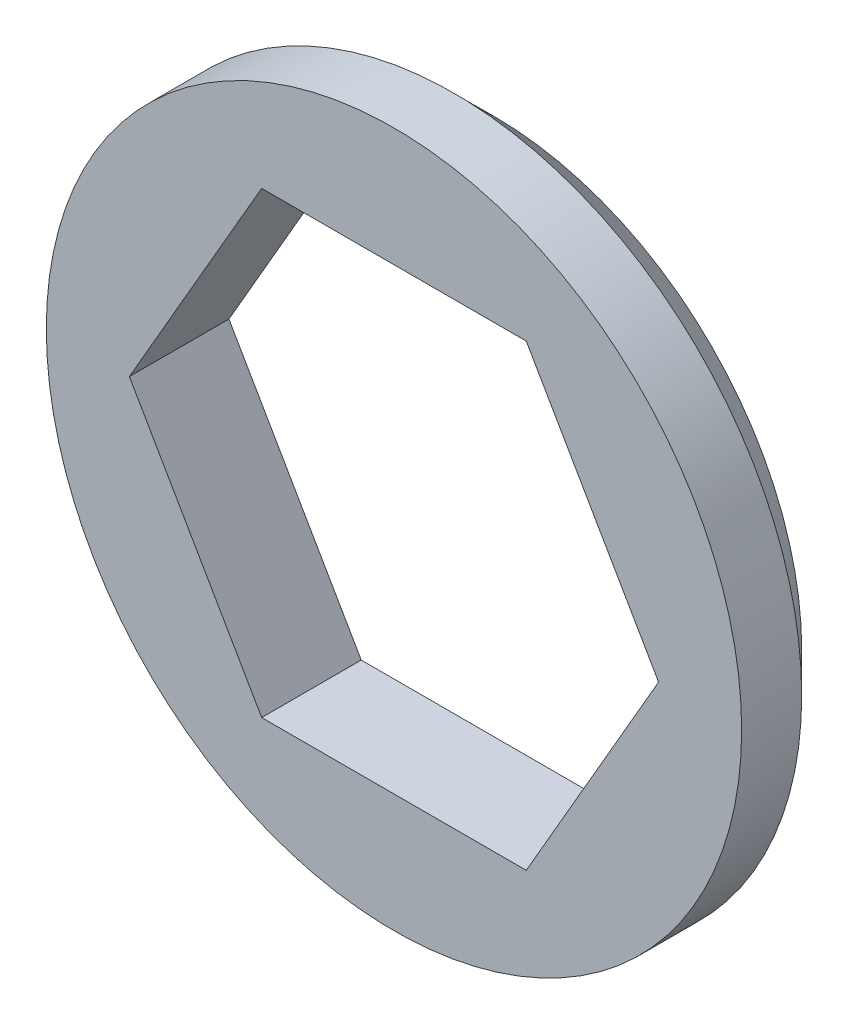
SolidWorks part; units mm, degrees
ref_plane "Front Plane" through (0, 0, 0) normal (0, 0, 1) x (1, 0, 0)
ref_plane "Top Plane" through (0, 0, 0) normal (0, 1, 0) x (1, 0, 0)
ref_plane "Right Plane" through (0, 0, 0) normal (1, 0, 0) x (0, 0, -1)
sketch "Sketch1" plane through (0, 0, 0) normal (0, 0, 1) x (1, 0, 0)
  line L0 (0, 0) -> (8.3716, 0) construction
  line L1 (8.3716, 0) -> (4.1858, 7.25)
  line L2 (4.1858, 7.25) -> (-4.1858, 7.25)
  line L3 (-4.1858, 7.25) -> (-8.3716, 0)
  line L4 (-8.3716, 0) -> (-4.1858, -7.25)
  line L5 (-4.1858, -7.25) -> (4.1858, -7.25)
  line L6 (4.1858, -7.25) -> (8.3716, 0)
  circle A0 centre (0, 0) radius 11
  circle A2 centre (0, 0) radius 7.25 construction
  dimension "D1" = 22
  dimension "D2" = 14.5
extrude "Boss-Extrude1" add sketch "Sketch1" along normal blind 3.15
chamfer "Chamfer1" distance 1.25 angle 45 1 edges at (11, 0, 0)
